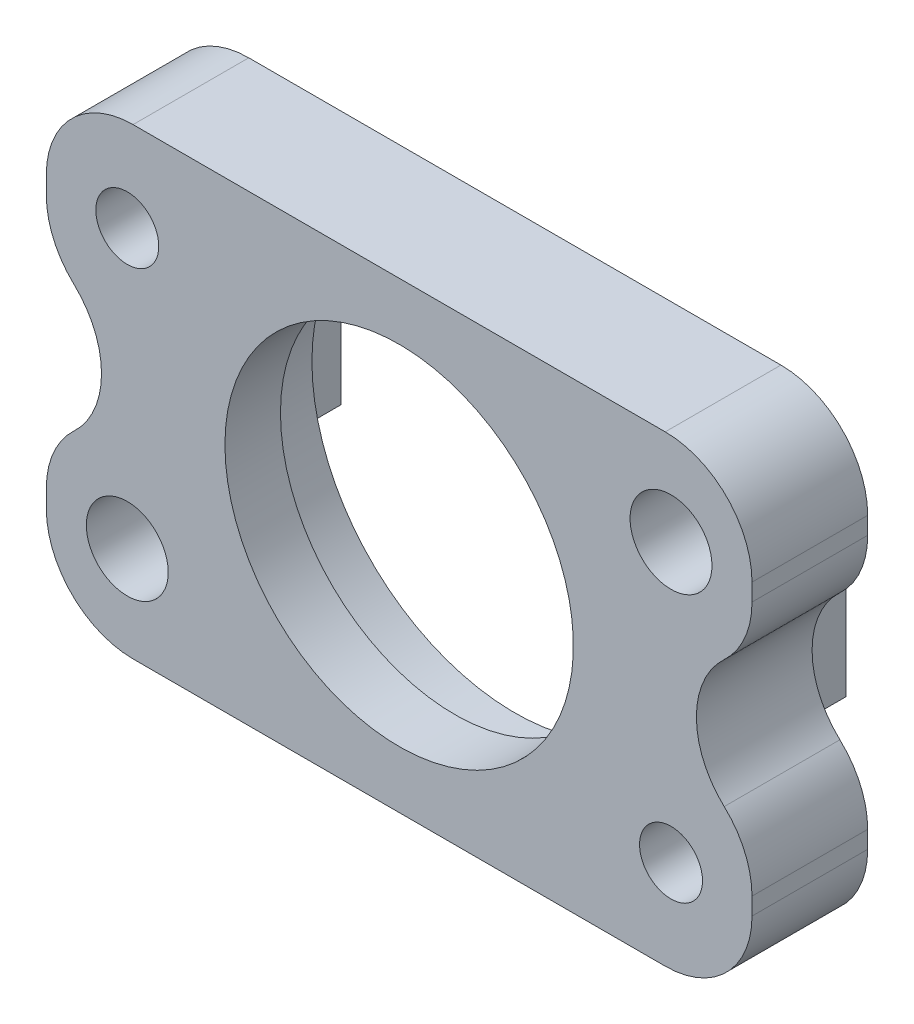
SolidWorks part; units mm, degrees
material "6061 Alloy"
ref_plane "Front Plane" through (0, 0, 0) normal (0, 0, 1) x (1, 0, 0)
ref_plane "Top Plane" through (0, 0, 0) normal (0, 1, 0) x (1, 0, 0)
ref_plane "Right Plane" through (0, 0, 0) normal (1, 0, 0) x (0, 0, -1)
ref_plane "Plane1" through (0, 0, 6.35) normal (0, 0, 1) x (1, 0, 0)
sketch "Sketch1" plane through (0, 0, 6.35) normal (0, 0, 1) x (1, 0, 0)
  line L0 (-254, 12.7) -> (-215.265, 12.7)
  line L1 (-215.265, 12.7) -> (-215.265, 38.1)
  line L2 (-215.265, 38.1) -> (-254, 38.1)
  line L3 (-254, 38.1) -> (-254, 12.7)
  dimension "D1" = 38.735
  dimension "D2" = 25.4
extrude "Boss-Extrude1" add sketch "Sketch1" against normal blind 6.35
sketch "Sketch2" plane through (0, 0, 0) normal (0, 0, -1) x (-1, 0, 0)
  line L0 (215.265, 32.3882) -> (215.265, 18.4118)
  line L1 (254, 38.1) -> (254, 12.7) construction
  line L2 (215.265, 38.1) -> (254, 38.1) construction
  arc A0 (215.265, 18.4118) -> (216.7914, 21.9059) centre (220.0275, 18.4118) cw
  arc A1 (216.7914, 21.9059) -> (216.7914, 28.8941) centre (213.5552, 25.4) ccw
  arc A2 (216.7914, 28.8941) -> (215.265, 32.3882) centre (220.0275, 32.3882) cw
  dimension "D1" = 4.7625
  dimension "D2" = 4.7625
  dimension "D3" = 33.9725
  dimension "D4" = 37.2086
  dimension "D5" = 5.7118
extrude "Cut-Extrude1" cut sketch "Sketch2" against normal through all
sketch "Sketch3" plane through (0, 0, 0) normal (0, 0, -1) x (-1, 0, 0)
  line L0 (254, 20.955) -> (254, 29.845)
  line L1 (215.265, 32.3882) -> (215.265, 38.1) construction
  arc A0 (254, 29.845) -> (254, 20.955) centre (255.7449, 25.4) ccw
  dimension "D1" = 4.7752
  dimension "D2" = 38.735
  dimension "D3" = 40.4799
  dimension "D4" = 8.255
extrude "Cut-Extrude2" cut sketch "Sketch3" against normal through all
sketch "Sketch4" plane through (0, 0, 0) normal (0, 0, -1) x (-1, 0, 0)
  line L0 (221.9071, 20.955) -> (219.6211, 20.955)
  line L1 (219.6211, 20.955) -> (219.6211, 29.845)
  line L2 (219.6211, 29.845) -> (221.9071, 29.845)
  line L3 (221.9071, 29.845) -> (221.9071, 20.955)
  line L4 (254, 38.1) -> (254, 29.845) construction
  line L5 (215.265, 38.1) -> (254, 38.1) construction
  dimension "D1" = 32.0929
  dimension "D2" = 34.3789
  dimension "D3" = 8.255
  dimension "D4" = 17.145
extrude "Boss-Extrude2" add sketch "Sketch4" along normal blind 3.175
sketch "Sketch5" plane through (0, 0, 0) normal (0, 0, -1) x (-1, 0, 0)
  line L0 (249.6439, 20.955) -> (247.3579, 20.955)
  line L1 (247.3579, 20.955) -> (247.3579, 29.845)
  line L2 (247.3579, 29.845) -> (249.6439, 29.845)
  line L3 (249.6439, 29.845) -> (249.6439, 20.955)
  line L4 (254, 38.1) -> (254, 29.845) construction
  line L5 (215.265, 38.1) -> (254, 38.1) construction
  dimension "D1" = 4.3561
  dimension "D2" = 6.6421
  dimension "D3" = 8.255
  dimension "D4" = 17.145
extrude "Boss-Extrude3" add sketch "Sketch5" along normal blind 3.175
hole_wizard "Hole1" positions "Sketch7" profile "Sketch6" legacy
sketch "Sketch7" plane through (0, 0, 0) normal (0, 0, -1) x (-1, 0, 0)
  point P0 (234.6325, 25.4)
sketch "Sketch6" plane through (-234.6325, 25.4, 0) normal (1, 0, 0) x (0, 1, 0)
  line L0 (0, 0) -> (0, 6.35)
  line L1 (0, 6.35) -> (9.5631, 6.35)
  line L2 (9.5631, 6.35) -> (9.5631, 3.302)
  line L3 (9.5631, 3.302) -> (11.1379, 3.302)
  line L4 (11.1379, 3.302) -> (11.1379, 0)
  line L5 (11.1379, 0) -> (0, 0)
  line L6 (0, 110) -> (0, -10) construction
  dimension "Diameter" = 19.1262
  dimension "Depth" = 6.35
  dimension "C-Bore Diameter" = 22.2758
  dimension "C-Bore Depth" = 3.302
hole_wizard "#16 (0.177) Diameter Hole1" positions "Sketch9" profile "Sketch8" hole size "#16" standard "ANSI Inch"
sketch "Sketch9" plane through (0, 0, 6.35) normal (0, 0, 1) x (1, 0, 0)
  point P0 (-249.555, 17.78)
  point P1 (-219.71, 33.02)
sketch "Sketch8" plane through (-249.555, 17.78, 6.35) normal (1, 0, 0) x (0, -1, 0)
  line L0 (0, 0) -> (0, 9.525)
  line L1 (0, 9.525) -> (2.2479, 9.525)
  line L2 (2.2479, 9.525) -> (2.2479, 0)
  line L5 (2.2479, 0) -> (0, 0)
  line L11 (0, -6.35) -> (0, 107.95) construction
  dimension "Thru Hole Dia." = 4.4958
  dimension "Thru Hole Depth" = 9.525
hole_wizard "#29 (0.136) Diameter Hole1" positions "Sketch11" profile "Sketch10" hole size "#29" standard "ANSI Inch"
sketch "Sketch11" plane through (0, 0, 6.35) normal (0, 0, 1) x (1, 0, 0)
  point P0 (-219.71, 17.78)
  point P1 (-249.555, 33.02)
sketch "Sketch10" plane through (-219.71, 17.78, 6.35) normal (1, 0, 0) x (0, -1, 0)
  line L0 (0, 0) -> (0, 9.525)
  line L1 (0, 9.525) -> (1.7272, 9.525)
  line L2 (1.7272, 9.525) -> (1.7272, 0)
  line L5 (1.7272, 0) -> (0, 0)
  line L11 (0, -6.35) -> (0, 107.95) construction
  dimension "Thru Hole Dia." = 3.4544
  dimension "Thru Hole Depth" = 9.525
fillet "Fillet1" radius 4.7625 6 edges at (-254, 20.955, 3.175) (-254, 29.845, 3.175) (-215.265, 12.7, 3.175) (-254, 12.7, 3.175) (-215.265, 38.1, 3.175) (-254, 38.1, 3.175)
